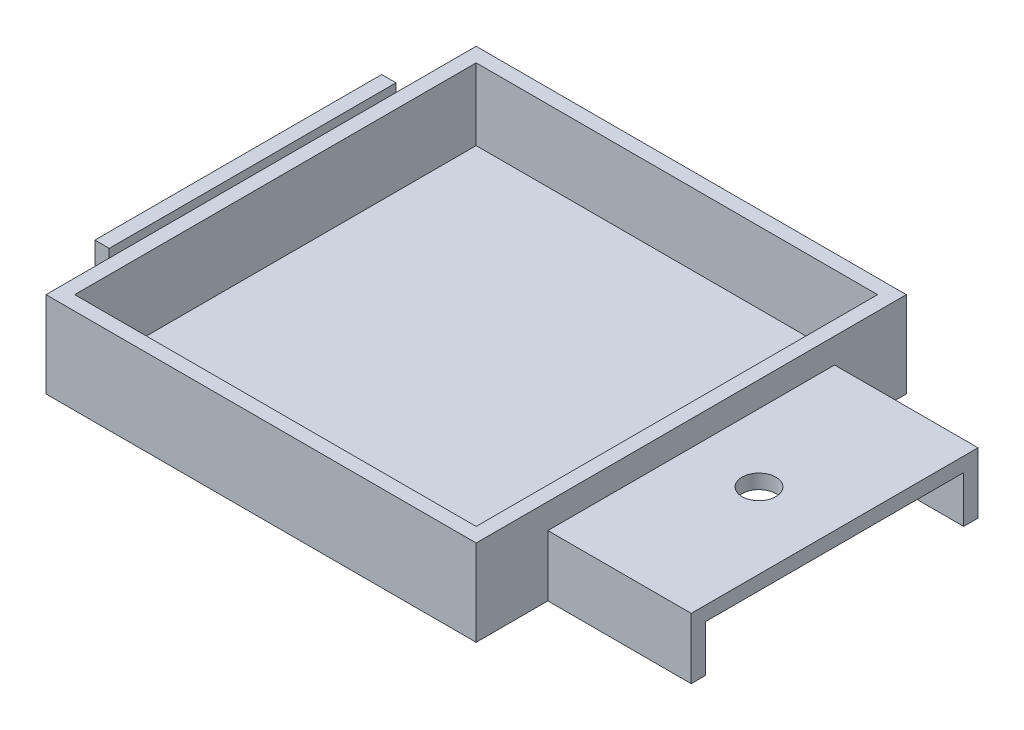
SolidWorks part; units mm, degrees
ref_plane "Front Plane" through (0, 0, 0) normal (0, 0, 1) x (1, 0, 0)
ref_plane "Top Plane" through (0, 0, 0) normal (0, 1, 0) x (1, 0, 0)
ref_plane "Right Plane" through (0, 0, 0) normal (1, 0, 0) x (0, 0, -1)
sketch "Sketch1" plane through (0, 0, 0) normal (0, 1, 0) x (1, 0, 0)
  line L1 (0, 0) -> (76.2, 0)
  line L2 (0, 0) -> (0, 76.2)
  line L3 (0, 76.2) -> (76.2, 76.2)
  line L4 (76.2, 0) -> (76.2, 76.2)
  dimension "D1" = 76.2
  dimension "D2" = 76.2
extrude "Boss-Extrude1" add sketch "Sketch1" along normal blind 2.54
sketch "Sketch2" plane through (0, 2.54, 0) normal (0, 1, 0) x (1, 0, 0)
  line L1 (0, 76.2) -> (76.2, 76.2)
  line L2 (0, 76.2) -> (0, 0)
  line L3 (0, 0) -> (76.2, 0)
  line L4 (76.2, 76.2) -> (76.2, 0)
  line L5 (2.54, 73.66) -> (73.66, 73.66)
  line L6 (2.54, 73.66) -> (2.54, 2.54)
  line L7 (2.54, 2.54) -> (73.66, 2.54)
  line L8 (73.66, 73.66) -> (73.66, 2.54)
  point P10 (38.1, 73.66)
  point P11 (38.1, 76.2)
  point P12 (2.54, 38.1)
  point P13 (0, 38.1)
  dimension "D1" = 2.54
  dimension "D2" = 2.54
extrude "Boss-Extrude2" add sketch "Sketch2" along normal blind 12.7
sketch "Sketch3" plane through (76.2, 0, 0) normal (1, 0, 0) x (0, 0, -1)
  line L0 (0, 0) -> (76.2, 0) construction
  line L6 (12.7, 10.795) -> (63.5, 10.795)
  line L7 (12.7, 10.795) -> (12.7, 8.255)
  line L8 (12.7, 8.255) -> (63.5, 8.255)
  line L9 (63.5, 10.795) -> (63.5, 8.255)
  point P6 (38.1, 0)
  point P7 (38.1, 8.255)
  dimension "D1" = 2.54
  dimension "D2" = 50.8
  dimension "D3" = 8.255
extrude "Boss-Extrude3" add sketch "Sketch3" along normal blind 25.4
sketch "Sketch5" plane through (0, 10.795, 0) normal (0, 1, 0) x (1, 0, 0)
  line L0 (76.2, 0) -> (76.2, 76.2) construction
  line L1 (101.6, 63.5) -> (101.6, 12.7) construction
  circle A0 centre (88.2, 38.1) radius 3
  point P4 (0, 0)
  point P7 (101.6, 38.1)
  dimension "D1" = 6
  dimension "D2" = 12
extrude "Cut-Extrude2" cut sketch "Sketch5" against normal through all
sketch "Sketch6" plane through (0, 8.255, 0) normal (0, -1, 0) x (1, 0, 0)
  line L0 (76.2, -12.7) -> (101.6, -12.7)
  line L2 (101.6, -63.5) -> (76.2, -63.5)
  line L3 (76.2, -63.5) -> (76.2, -60.96)
  line L4 (76.2, 0) -> (76.2, -76.2) construction
  line L5 (76.2, -60.96) -> (101.6, -60.96)
  line L7 (101.6, -15.24) -> (76.2, -15.24)
  line L8 (76.2, -15.24) -> (76.2, -12.7)
  line L9 (101.6, -12.7) -> (101.6, -63.5) construction
  line L10 (101.6, -12.7) -> (101.6, -15.24)
  line L11 (101.6, -60.96) -> (101.6, -63.5)
  dimension "D1" = 2.54
  dimension "D3" = 2.54
extrude "Boss-Extrude4" add sketch "Sketch6" along normal up to surface (8.255 mm away) up to face at (38.1, 0, -38.1)
sketch "Sketch9" plane through (0, 0, 0) normal (-1, 0, 0) x (0, 0, 1)
  line L0 (-76.2, 0) -> (0, 0) construction
  line L1 (-63.5, 2.54) -> (-12.7, 2.54)
  line L2 (-63.5, 2.54) -> (-63.5, 0)
  line L3 (-63.5, 0) -> (-12.7, 0)
  line L4 (-12.7, 2.54) -> (-12.7, 0)
  point P6 (-38.1, 0)
  point P7 (-38.1, 0)
  dimension "D1" = 2.54
  dimension "D2" = 50.8
extrude "Boss-Extrude5" add sketch "Sketch9" along normal blind 1.5
sketch "Sketch10" plane through (-1.5, 0, 0) normal (-1, 0, 0) x (0, 0, 1)
  line L0 (-12.7, 0) -> (-12.7, 2.54) construction
  line L1 (-63.5, 0) -> (-12.7, 0)
  line L2 (-63.5, 0) -> (-63.5, 15.24)
  line L3 (-63.5, 15.24) -> (-12.7, 15.24)
  line L4 (-12.7, 0) -> (-12.7, 15.24)
  line L5 (-76.2, 15.24) -> (0, 15.24) construction
extrude "Boss-Extrude6" add sketch "Sketch10" along normal blind 2.54
